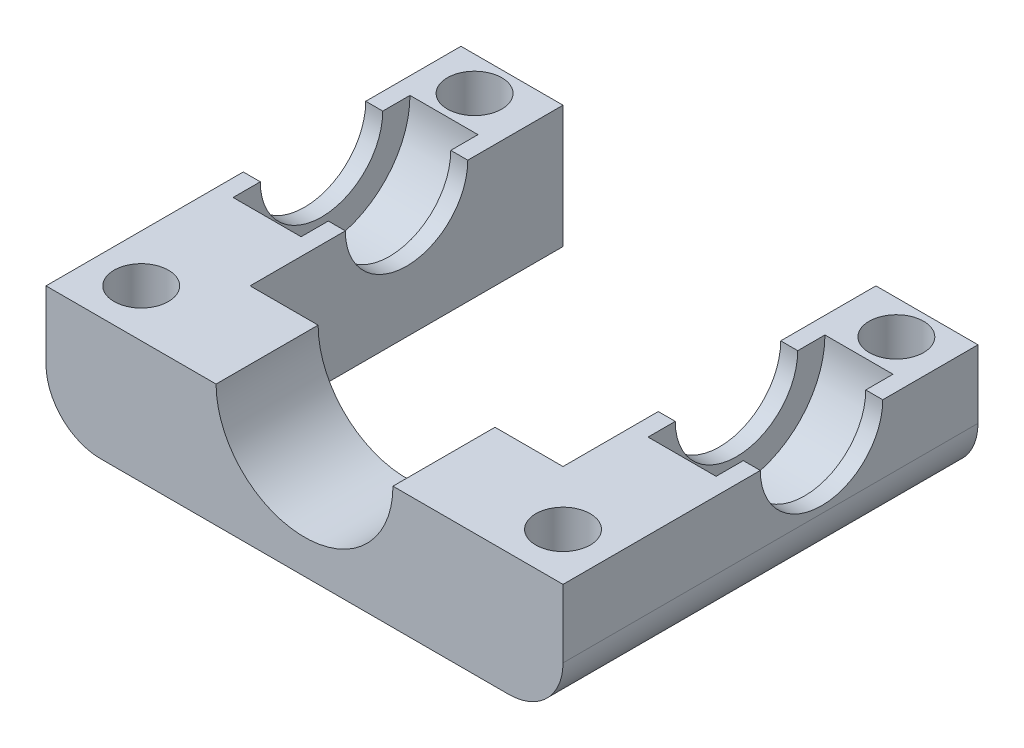
SolidWorks part; units mm, degrees
ref_plane "Front Plane" through (0, 0, 0) normal (0, 0, 1) x (1, 0, 0)
ref_plane "Top Plane" through (0, 0, 0) normal (0, 1, 0) x (1, 0, 0)
ref_plane "Right Plane" through (0, 0, 0) normal (1, 0, 0) x (0, 0, -1)
sketch "Sketch1" plane through (0, 0, 0) normal (0, 1, 0) x (1, 0, 0)
  line L2 (-19, 11.5) -> (-19, -19)
  line L3 (-19, -19) -> (19, -19)
  line L4 (19, 11.5) -> (19, -19)
  line L5 (-11.5, 11.5) -> (19, -19) construction
  line L6 (-19, -19) -> (11.5, 11.5) construction
  line L8 (-11.5, 11.5) -> (-11.5, -11.5)
  line L9 (-11.5, -11.5) -> (11.5, -11.5)
  line L10 (11.5, 11.5) -> (11.5, -11.5)
  line L11 (-11.5, 11.5) -> (11.5, -11.5) construction
  line L12 (-11.5, -11.5) -> (11.5, 11.5) construction
  line L13 (11.5, 11.5) -> (19, 11.5)
  line L14 (-11.5, 11.5) -> (-19, 11.5)
  point P0 (0, 0)
  point P6 (3.75, -3.75)
  dimension "D1" = 38
  dimension "D4" = 23
extrude "Boss-Extrude1" add sketch "Sketch1" along normal blind 9
ref_plane "Plane1" through (15.25, 0, 0) normal (1, 0, 0) x (0, 0, -1)
sketch "Sketch2" plane through (15.25, 0, 0) normal (1, 0, 0) x (0, 0, -1)
  line L1 (-19, 9) -> (-19, 0) construction
  circle A0 centre (0, 9) radius 6.5
  dimension "D1" = 13
  dimension "D2" = 19
extrude "Cut-Extrude1" cut sketch "Sketch2" against normal blind 2.5 and the other way blind 2.5
sketch "Sketch3" plane through (0, 0, 0) normal (1, 0, 0) x (0, 0, -1)
  line L1 (0, 9) -> (0, 0) construction
  circle A0 centre (0, 9) radius 4.5
  dimension "D1" = 9
extrude "Cut-Extrude2" cut sketch "Sketch3" along normal through all
mirror "Mirror1" about plane through (0, 0, 0) normal (1, 0, 0) of "Cut-Extrude1", "Cut-Extrude2"
sketch "Sketch5" plane through (0, 0, -11.5) normal (0, 0, -1) x (-1, 0, 0)
  line L0 (0, 0) -> (0, 9) construction
  circle A0 centre (0, 9) radius 22.5
  dimension "D1" = 45
  dimension "D2" = 9
fillet "Fillet1" radius 4 2 edges at (-19, 0, 3.75) (19, 0, 3.75)
sketch "Sketch4" plane through (0, 0, 0) normal (0, 0, 1) x (1, 0, 0)
  line L0 (-19, 9) -> (19, 9) construction
  circle A0 centre (0, 9) radius 6.5
  dimension "D1" = 13
extrude "Cut-Extrude3" cut sketch "Sketch4" along normal through all both and the other way through all
sketch "Sketch6" plane through (0, 9, 0) normal (0, 1, 0) x (1, 0, 0)
  line L0 (-15.5, 9) -> (15.5, 9) construction
  line L1 (15.5, 9) -> (15.5, -15.5) construction
  line L2 (15.5, -15.5) -> (-15.5, -15.5) construction
  line L3 (-15.5, -15.5) -> (-15.5, 9) construction
  line L4 (-19, -4.5) -> (-19, -19) construction
  line L5 (19, -19) -> (19, -4.5) construction
  line L6 (6.5, -19) -> (19, -19) construction
  line L7 (19, 11.5) -> (11.5, 11.5) construction
  circle A0 centre (-15.5, 9) radius 2
  circle A1 centre (15.5, 9) radius 2
  circle A2 centre (15.5, -15.5) radius 2
  circle A3 centre (-15.5, -15.5) radius 2
  dimension "D1" = 3.5
  dimension "D2" = 3.5
  dimension "D3" = 3.5
  dimension "D4" = 2.5
extrude "Cut-Extrude4" cut sketch "Sketch6" against normal through all
